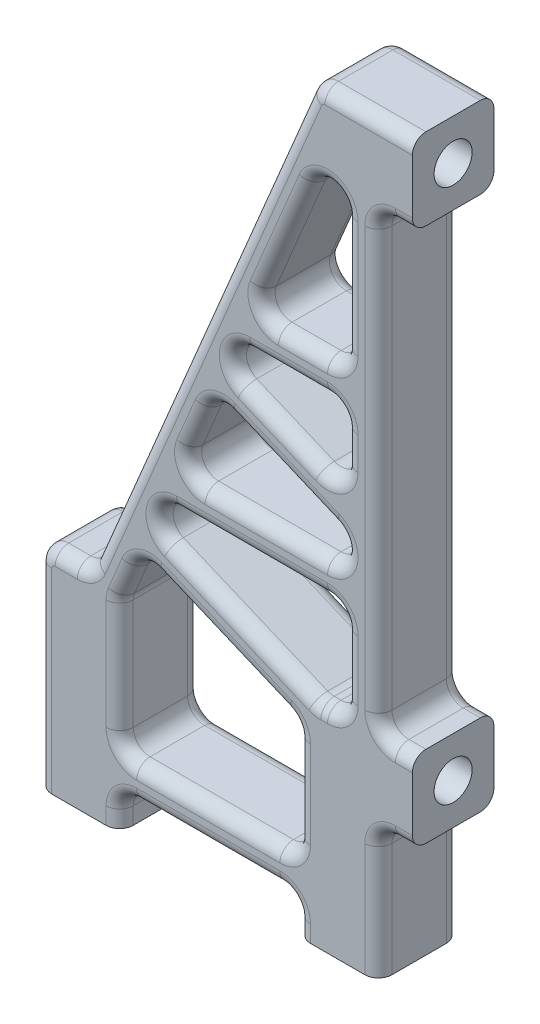
SolidWorks part; units mm, degrees
ref_plane "Спереди" through (0, 0, 0) normal (0, 0, 1) x (1, 0, 0)
ref_plane "Сверху" through (0, 0, 0) normal (0, 1, 0) x (1, 0, 0)
ref_plane "Справа" through (0, 0, 0) normal (1, 0, 0) x (0, 0, -1)
sketch "Эскиз1" plane through (0, 0, 0) normal (0, 0, 1) x (1, 0, 0)
  line L0 (-18.4277, 52) -> (76.1089, 52) construction
  line L1 (-18.4277, 12.63) -> (76.1089, 12.63) construction
  line L2 (-18.4277, 6.28) -> (76.1089, 6.28) construction
  line L3 (3, 87.6877) -> (3, -19.2431) construction
  line L4 (22.05, 87.6877) -> (22.05, -19.2431) construction
  line L5 (27.55, 49) -> (27.55, 55)
  line L6 (19.05, 0) -> (25.05, 0)
  line L7 (0, 0) -> (6, 0)
  line L8 (25.05, 0) -> (25.05, 8.38)
  line L9 (27.55, 9.63) -> (27.55, 15.63)
  line L10 (25.05, 47.75) -> (25.05, 16.88)
  line L11 (7.25, 2.5) -> (17.8, 2.5)
  line L12 (0, 0) -> (0, 14.38)
  line L13 (4.0295, 16.3949) -> (19.9616, 54.2351)
  line L14 (21.1137, 55) -> (27.55, 55)
  line L15 (19.05, 6.25) -> (19.05, 14.38)
  line L16 (17.8, 5) -> (7.25, 5)
  line L17 (6, 6.25) -> (6, 14.38)
  line L18 (6.0979, 14.8651) -> (20.1479, 48.2351)
  line L19 (20.3, 15.63) -> (21.3, 15.63)
  line L20 (22.55, 16.88) -> (22.55, 47.75)
  line L21 (28.4544, 49) -> (19.3381, 49) construction
  line L22 (27.55, 49) -> (26.3, 49)
  line L23 (27.55, 15.63) -> (26.3, 15.63)
  line L24 (27.55, 9.63) -> (26.3, 9.63)
  line L25 (19.05, 0) -> (19.05, 1.25)
  line L26 (6, 0) -> (6, 1.25)
  line L27 (1.25, 15.63) -> (2.8775, 15.63)
  arc A0 (26.3, 49) -> (25.05, 47.75) centre (26.3, 47.75) ccw
  arc A1 (25.05, 16.88) -> (26.3, 15.63) centre (26.3, 16.88) ccw
  arc A2 (25.05, 8.38) -> (26.3, 9.63) centre (26.3, 8.38) cw
  arc A3 (6, 1.25) -> (7.25, 2.5) centre (7.25, 1.25) cw
  arc A4 (17.8, 2.5) -> (19.05, 1.25) centre (17.8, 1.25) cw
  arc A5 (1.25, 15.63) -> (0, 14.38) centre (1.25, 14.38) ccw
  arc A6 (19.9616, 54.2351) -> (21.1137, 55) centre (21.1137, 53.75) cw
  arc A7 (19.05, 6.25) -> (17.8, 5) centre (17.8, 6.25) cw
  arc A8 (7.25, 5) -> (6, 6.25) centre (7.25, 6.25) cw
  arc A9 (20.1479, 48.2351) -> (22.55, 47.75) centre (21.3, 47.75) cw
  arc A10 (6, 14.38) -> (6.0979, 14.8651) centre (7.25, 14.38) cw
  arc A11 (19.05, 14.38) -> (20.3, 15.63) centre (20.3, 14.38) cw
  arc A12 (21.3, 15.63) -> (22.55, 16.88) centre (21.3, 16.88) ccw
  arc A13 (2.8775, 15.63) -> (4.0295, 16.3949) centre (2.8775, 16.88) ccw
  point P13 (27.55, 52)
  point P16 (22.05, 0)
  point P19 (3, 0)
  point P31 (27.55, 12.63)
  dimension "D6" = 1.25
  dimension "D7" = 1.25
  dimension "D9" = 2.5
  dimension "D1" = 39.37
  dimension "D2" = 6.35
  dimension "D3" = 19.05
  dimension "D4" = 52
  dimension "D5" = 6
  dimension "D8" = 2.5
  dimension "D10" = 2.5
  dimension "D11" = 2.5
  dimension "D12" = 2.5
extrude "Бобышка-Вытянуть1" add sketch "Эскиз1" along normal blind 6
sketch "Эскиз2" plane through (0, 0, 0) normal (0, 0, 1) x (1, 0, 0)
  line L0 (7.5779, 18.3802) -> (19.05, 13.55)
  line L2 (20.5524, 15.63) -> (9.7001, 20.1992)
  line L5 (20.7851, 15.5321) -> (19.8149, 13.2279) construction
  line L6 (20.3, 15.63) -> (20.5524, 15.63)
  line L7 (10.1852, 22.6013) -> (22.55, 22.6013)
  line L8 (7.5779, 18.3802) -> (10.4078, 25.1013)
  line L9 (10.4078, 25.1013) -> (21.3, 25.1013)
  line L10 (12.98, 31.2106) -> (21.7851, 27.5033)
  line L11 (15.1022, 33.0296) -> (22.55, 29.8938)
  line L12 (22.55, 35.4317) -> (15.5872, 35.4317)
  line L13 (15.8098, 37.9317) -> (22.55, 37.9317)
  line L14 (22.55, 16.88) -> (22.55, 47.75) construction
  line L17 (22.55, 37.9317) -> (22.55, 35.4317)
  line L18 (15.8098, 37.9317) -> (12.98, 31.2106)
  line L19 (22.55, 29.8938) -> (22.55, 22.6013)
  line L21 (20.1479, 48.2351) -> (6.0979, 14.8651) construction
  line L22 (20.3, 15.63) -> (21.3, 15.63) construction
  line L23 (19.05, 14.38) -> (19.05, 13.55)
  line L24 (19.05, 6.25) -> (19.05, 14.38) construction
  arc A1 (19.05, 14.38) -> (20.3, 15.63) centre (20.3, 14.38) cw
  arc A2 (9.7001, 20.1992) -> (10.1852, 22.6013) centre (10.1852, 21.3513) cw
  arc A3 (21.3, 25.1013) -> (21.7851, 27.5033) centre (21.3, 26.3513) ccw
  arc A4 (15.5872, 35.4317) -> (15.1022, 33.0296) centre (15.5872, 34.1817) ccw
  arc A6 (20.3, 15.63) -> (19.05, 14.38) centre (20.3, 14.38) ccw construction
  point P6 (20.3, 14.38)
  point P9 (20.3, 14.38)
  dimension "D2" = 1.25
  dimension "D1" = 2.5
  dimension "D3" = 2.5
  dimension "D4" = 2.5
  dimension "D5" = 2.5
extrude "Бобышка-Вытянуть2" add sketch "Эскиз2" along normal blind 6
fillet "Скругление1" radius 1.25 10 edges at (19.05, 13.55, 3) (20.5524, 15.63, 3) (7.5779, 18.3802, 3) (22.55, 22.6013, 3) (10.4078, 25.1013, 3) (12.98, 31.2106, 3) (22.55, 29.8938, 3) (22.55, 35.4317, 3) (15.8098, 37.9317, 3) (22.55, 37.9317, 3)
sketch "Эскиз3" plane through (27.55, 0, 0) normal (1, 0, 0) x (0, 0, -1)
  line L0 (-6, 9.63) -> (0, 15.63) construction
  line L1 (0, 9.63) -> (-6, 15.63) construction
  line L2 (-6, 49) -> (0, 55) construction
  line L3 (0, 49) -> (-6, 55) construction
  circle A0 centre (-3, 52) radius 1.4
  circle A1 centre (-3, 12.63) radius 1.4
  point P12 (-3, 12.63)
  point P21 (-3, 52)
  dimension "D1" = 2.8
extrude "Вырез-Вытянуть1" cut sketch "Эскиз3" against normal blind 7 contours A1 | A0
sketch "Эскиз4" plane through (0, 0, 0) normal (0, -1, 0) x (1, 0, 0)
  line L0 (25.05, 6) -> (19.05, 0) construction
  line L1 (19.05, 6) -> (25.05, 0) construction
  line L2 (0, 6) -> (6, 0) construction
  line L3 (6, 6) -> (0, 0) construction
  circle A0 centre (3, 3) radius 1.4
  circle A1 centre (22.05, 3) radius 1.4
  point P16 (3, 3)
  point P17 (22.05, 3)
  dimension "D1" = 2.8
extrude "Вырез-Вытянуть2" cut sketch "Эскиз4" against normal blind 7
fillet "Скругление7" radius 1 112 edges at (21.5474, 48.9753, 0) (21.5474, 48.9753, 6) (14.362, 34.4291, 0) (14.362, 34.4291, 6) (18.4436, 35.4317, 0) (18.4436, 35.4317, 6) (17.9586, 29.1144, 6) (17.9586, 29.1144, 0) (22.5253, 26.1039, 0) (22.5253, 26.1039, 6) (15.0099, 17.9636, 6) (15.0099, 17.9636, 0) (8.9599, 21.5987, 0) (8.9599, 21.5987, 6) (15.7426, 22.6013, 0) (15.7426, 22.6013, 6) (6, 0.625, 0) (6, 0.625, 6) (24.3318, 55, 0) (24.3318, 55, 6) (20.4222, 54.7914, 0) (20.4222, 54.7914, 6) (0, 7.19, 0) (0, 7.19, 6) (19.4962, 37.9317, 0) (19.4962, 37.9317, 6) (17.9586, 31.827, 6) (17.9586, 31.827, 0) (16.7952, 25.1013, 0) (16.7952, 25.1013, 6) (25.05, 32.315, 0) (25.05, 32.315, 6) (25.05, 4.19, 0) (25.05, 4.19, 6) (12.525, 2.5, 0) (12.525, 2.5, 6) (11.9956, 35.315, 0) (11.9956, 35.315, 6) (16.6511, 38.4902, 6) (16.6511, 38.4902, 0) (18.3442, 43.9509, 0) (18.3442, 43.9509, 6) (22.55, 43.4658, 0) (22.55, 43.4658, 6) (22.1839, 38.2978, 6) (22.1839, 38.2978, 0) (22.1839, 35.0656, 6) (22.1839, 35.0656, 0) (22.55, 32.979, 0) (22.55, 32.979, 6) (21.9914, 30.735, 6) (21.9914, 30.735, 0) (11.249, 25.6598, 6) (11.249, 25.6598, 0) (11.8166, 28.4474, 0) (11.8166, 28.4474, 6) (13.1754, 30.7311, 6) (13.1754, 30.7311, 0) (20.5574, 15.6547, 6) (20.5574, 15.6547, 0) (21.0524, 15.63, 0) (21.0524, 15.63, 6) (22.1839, 15.9961, 0) (22.1839, 15.9961, 6) (22.55, 19.1156, 0) (22.55, 19.1156, 6) (22.1839, 22.2352, 6) (22.1839, 22.2352, 0) (6.3661, 5.3661, 0) (6.3661, 5.3661, 6) (6, 10.315, 0) (6, 10.315, 6) (6.0247, 14.6274, 0) (6.0247, 14.6274, 6) (6.5954, 16.0466, 0) (6.5954, 16.0466, 6) (7.7733, 17.9007, 6) (7.7733, 17.9007, 0) (13.5075, 15.8836, 0) (13.5075, 15.8836, 6) (18.8414, 13.4115, 6) (18.8414, 13.4115, 0) (19.05, 9.485, 6) (19.05, 9.485, 0) (18.6839, 5.3661, 0) (18.6839, 5.3661, 6) (12.525, 5, 0) (12.525, 5, 6) (0.3661, 15.2639, 0) (0.3661, 15.2639, 6) (2.0637, 15.63, 0) (2.0637, 15.63, 6) (3.5689, 15.8386, 0) (3.5689, 15.8386, 6) (6.3661, 2.1339, 0) (6.3661, 2.1339, 6) (19.05, 0.625, 0) (19.05, 0.625, 6) (18.6839, 2.1339, 0) (18.6839, 2.1339, 6) (26.925, 9.63, 0) (26.925, 9.63, 6) (25.4161, 9.2639, 0) (25.4161, 9.2639, 6) (26.925, 15.63, 0) (26.925, 15.63, 6) (25.4161, 15.9961, 0) (25.4161, 15.9961, 6) (26.925, 49, 0) (26.925, 49, 6) (25.4161, 48.6339, 0) (25.4161, 48.6339, 6)
